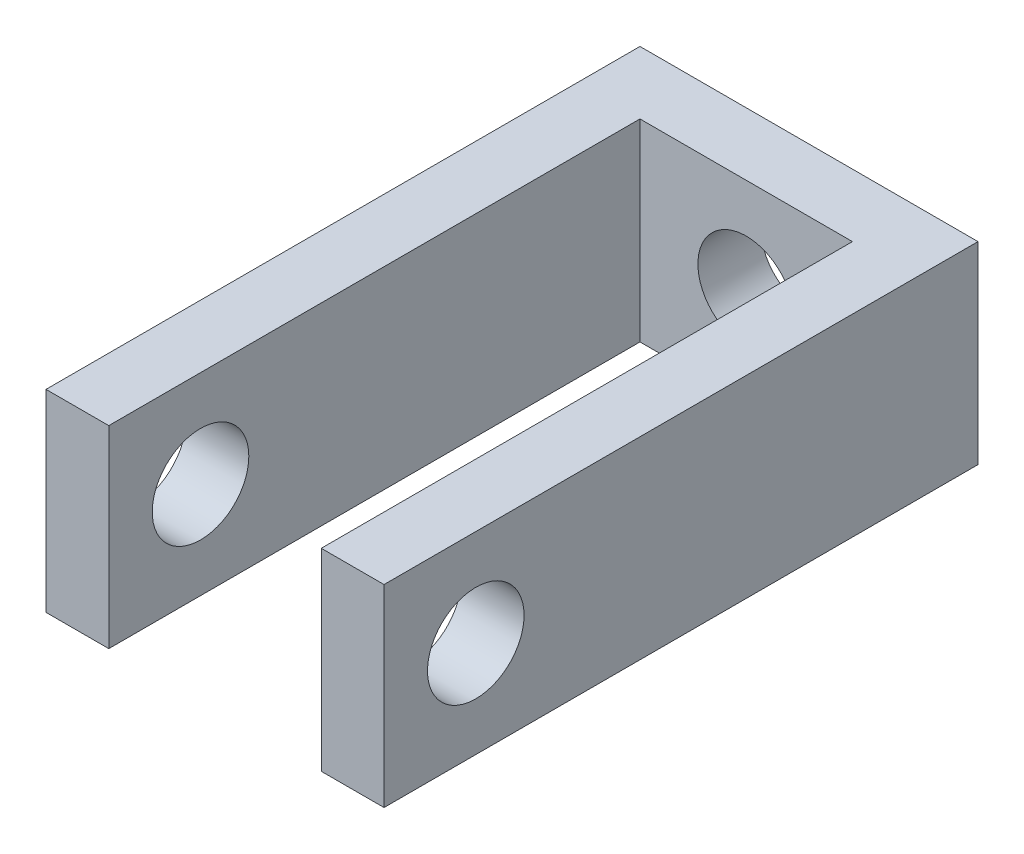
SolidWorks part; units mm, degrees
ref_plane "Front" through (0, 0, 0) normal (0, 0, 1) x (1, 0, 0)
ref_plane "Top" through (0, 0, 0) normal (0, 1, 0) x (1, 0, 0)
ref_plane "Right" through (0, 0, 0) normal (1, 0, 0) x (0, 0, -1)
sketch "草图1" plane through (0, 0, 0) normal (0, 0, 1) x (1, 0, 0)
  line L1 (0, 0) -> (7, 0)
  line L2 (0, 0) -> (0, 4)
  line L3 (0, 4) -> (7, 4)
  line L4 (7, 0) -> (7, 4)
extrude "凸台-拉伸1" add sketch "草图1" along normal blind 1.3
sketch "草图2" plane through (0, 0, 1.3) normal (0, 0, 1) x (1, 0, 0)
  line L12 (0, 0) -> (7, 0) construction
  line L13 (0, 4) -> (1.3, 4)
  line L14 (0, 4) -> (0, 0)
  line L15 (0, 0) -> (1.3, 0)
  line L16 (1.3, 4) -> (1.3, 0)
  line L18 (7, 4) -> (5.7, 4)
  line L19 (7, 4) -> (7, 0)
  line L20 (7, 0) -> (5.7, 0)
  line L21 (5.7, 4) -> (5.7, 0)
extrude "凸台-拉伸2" add sketch "草图2" along normal blind 11
sketch "草图3" plane through (0, 0, 1.3) normal (0, 0, 1) x (1, 0, 0)
  circle A0 centre (3.5, 2) radius 1
  point P2 (3.4872, 2.0568)
  point P3 (3.4872, 2)
  point P4 (3.5, 2)
extrude "切除-拉伸1" cut sketch "草图3" against normal blind 2
sketch "草图4" plane through (7, 0, 0) normal (1, 0, 0) x (0, 0, -1)
  line L1 (0, 0) -> (0, 4) construction
  circle A0 centre (-10.4, 2) radius 1
  dimension "D1" = 10.4
extrude "切除-拉伸2" cut sketch "草图4" against normal blind 7
